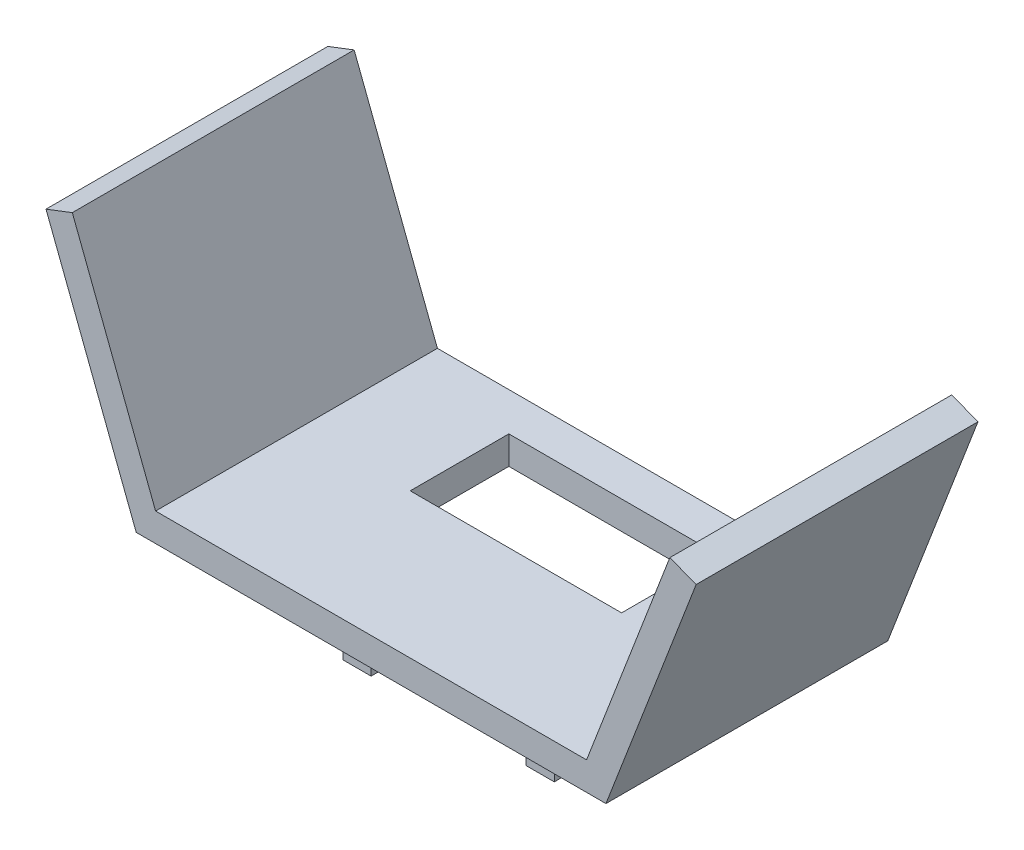
SolidWorks part; units mm, degrees
ref_plane "정면" through (0, 0, 0) normal (0, 0, 1) x (1, 0, 0)
ref_plane "윗면" through (0, 0, 0) normal (0, 1, 0) x (1, 0, 0)
ref_plane "우측면" through (0, 0, 0) normal (1, 0, 0) x (0, 0, -1)
sketch "Sketch1" plane through (0, 0, 0) normal (0, 0, 1) x (1, 0, 0)
  line L0 (0, -63.2998) -> (0, 75.2998) construction
  line L1 (50, 0) -> (-50, 0)
  line L2 (-50, 0) -> (-69.2068, 50)
  line L3 (-69.2068, 50) -> (-63.6058, 52.1515)
  line L4 (-63.6058, 52.1515) -> (-45.8774, 6)
  line L5 (-45.8774, 6) -> (45.8774, 6)
  line L6 (63.6058, 52.1515) -> (45.8774, 6)
  line L7 (69.2068, 50) -> (63.6058, 52.1515)
  line L8 (50, 0) -> (69.2068, 50)
  point P10 (0, 6)
  point P13 (0, 0)
  dimension "D1" = 6
  dimension "D2" = 6
  dimension "D3" = 50
  dimension "D4" = 50
extrude "Boss-Extrude1" add sketch "Sketch1" along normal blind 60
sketch "Sketch2" plane through (0, 0, 0) normal (0, -1, 0) x (1, 0, 0)
  line L0 (0, -18.0841) -> (0, 82.2959) construction
  line L1 (22.5, 8.1691) -> (-22.5, 8.1691)
  line L2 (-22.5, 8.1691) -> (-22.5, 29.1691)
  line L3 (-22.5, 29.1691) -> (22.5, 29.1691)
  line L4 (22.5, 8.1691) -> (22.5, 29.1691)
  point P8 (0, 29.1691)
  point P9 (0, 8.1691)
  dimension "D1" = 22.5
  dimension "D2" = 21
extrude "Cut-Extrude1" cut sketch "Sketch2" along direction (0, -1, 0) on the side against the normal blind 6
sketch "Sketch3" plane through (0, 0, 0) normal (0, -1, 0) x (1, 0, 0)
  line L0 (0, 82.2959) -> (0, -18.0841) construction
  line L1 (-22.5, 43.5) -> (-22.5, 37.5)
  line L2 (-22.5, 37.5) -> (-16.5, 37.5)
  line L3 (-16.5, 37.5) -> (-16.5, 43.5)
  line L4 (-16.5, 43.5) -> (-22.5, 43.5)
  line L6 (-50, 60) -> (50, 60) construction
  line L7 (16.5, 43.5) -> (22.5, 43.5)
  line L8 (16.5, 37.5) -> (16.5, 43.5)
  line L9 (22.5, 37.5) -> (16.5, 37.5)
  line L10 (22.5, 43.5) -> (22.5, 37.5)
  dimension "D1" = 6
  dimension "D2" = 6
  dimension "D3" = 16.5
  dimension "D4" = 16.5
extrude "Boss-Extrude2" add sketch "Sketch3" along normal blind 18
